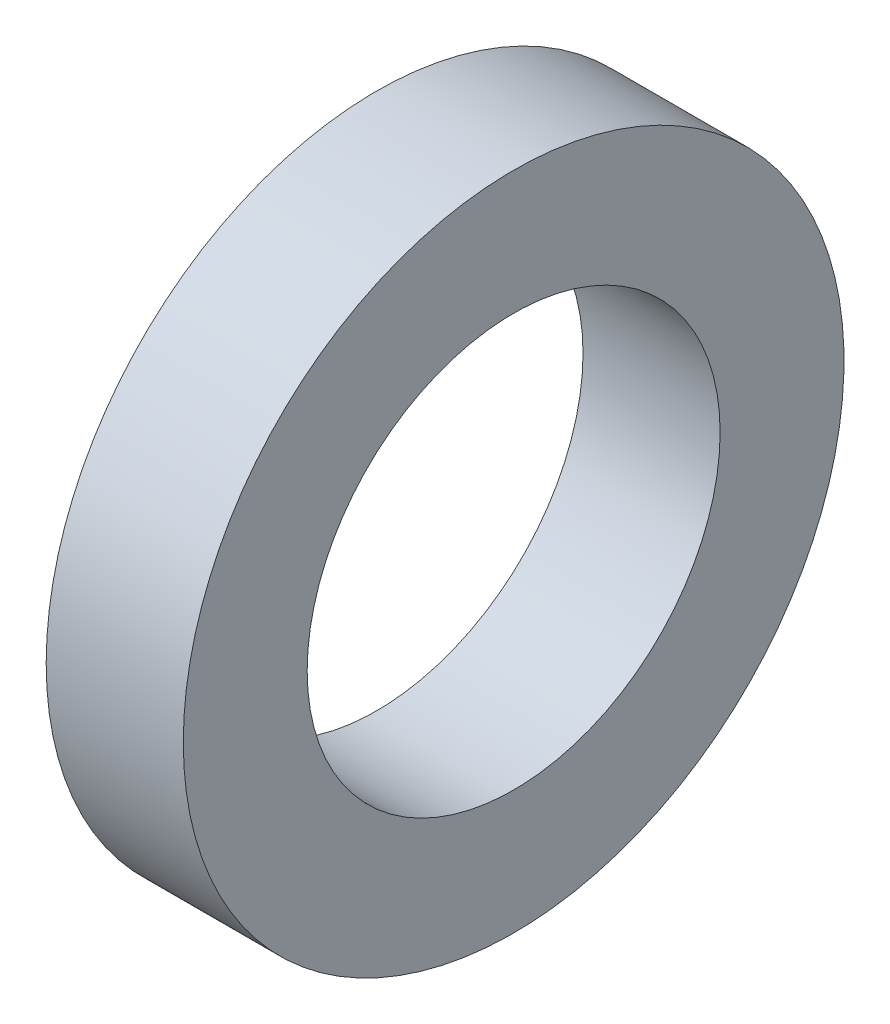
SolidWorks part; units mm, degrees
ref_plane "Front Plane" through (0, 0, 0) normal (0, 0, 1) x (1, 0, 0)
ref_plane "Top Plane" through (0, 0, 0) normal (0, 1, 0) x (1, 0, 0)
ref_plane "Right Plane" through (0, 0, 0) normal (1, 0, 0) x (0, 0, -1)
sketch "Sketch2" plane through (0, 0, 0) normal (0, 0, 1) x (1, 0, 0)
  line L0 (0, 0) -> (58.591, 0) construction
  line L2 (0, 0) -> (18.4, 0)
  line L3 (0, 0) -> (0, 2.5)
  line L4 (0, 2.5) -> (18.4, 2.5)
  line L5 (18.4, 0) -> (18.4, 2.5)
  line L6 (6.0094, 2.5) -> (6.0094, 6)
  line L11 (6.0094, 6) -> (9.9794, 6)
  line L16 (12.9794, 6) -> (12.9794, 3)
  line L17 (12.9794, 3) -> (13.6398, 3)
  line L18 (13.6398, 3) -> (13.6398, 2.5)
  line L19 (13.6398, 2.5) -> (6.0094, 2.5)
  line L22 (13.6398, 2.5) -> (16.1198, 2.5)
  line L23 (13.6398, 2.5) -> (13.6398, 4)
  line L24 (13.6398, 4) -> (16.1198, 4)
  line L25 (16.1198, 2.5) -> (16.1198, 4)
  line L27 (6.0094, 6) -> (9.9794, 6)
  line L28 (6.0094, 6) -> (6.0094, 9)
  line L29 (6.0094, 9) -> (9.9794, 9)
  line L30 (9.9794, 6) -> (9.9794, 9)
  line L31 (6.0094, 9) -> (6.0094, 8.25)
  line L32 (6.0094, 8.25) -> (5.0094, 8.25)
  line L33 (8.6609, 22.001) -> (8.6609, 12.476) construction
  line L34 (5.0094, 12.476) -> (12.3124, 12.476)
  line L35 (9.9794, 9) -> (12.3124, 9)
  line L36 (5.0094, 7.9375) -> (1.7709, 7.9375)
  line L37 (5.0094, 8.25) -> (5.0094, 12.476)
  line L38 (5.0094, 7.9375) -> (5.0094, 13.9365)
  line L39 (5.0094, 13.9365) -> (1.7709, 13.9365)
  line L40 (1.7709, 7.9375) -> (1.7709, 13.9365)
  line L41 (5.0094, 22.001) -> (12.3124, 22.001)
  line L42 (5.0094, 22.001) -> (5.0094, 30.1625)
  line L43 (5.0094, 30.1625) -> (12.3124, 30.1625)
  line L44 (12.3124, 22.001) -> (12.3124, 30.1625)
  line L49 (16.6398, 22.001) -> (16.6398, 7.5)
  line L51 (23.0198, 7.5) -> (23.0198, 6.5)
  line L54 (16.1198, 4) -> (13.6398, 4)
  line L56 (18.0398, 7.5) -> (23.0198, 7.5)
  line L57 (13.3124, 22.001) -> (16.6398, 22.001)
  line L58 (16.1198, 3.5) -> (20.0198, 3.5)
  line L59 (29.9098, 14) -> (26.9098, 11)
  line L60 (4.0094, 31.75) -> (18.0398, 31.75)
  line L61 (18.0398, 7.5) -> (23.0198, 7.5)
  line L62 (18.0398, 7.5) -> (18.0398, 12)
  line L63 (18.0398, 12) -> (23.0198, 12)
  line L64 (23.0198, 7.5) -> (23.0198, 12)
  line L65 (18.0398, 31.75) -> (18.0398, 12)
  line L66 (23.0198, 11) -> (26.9098, 11)
  line L67 (34.8098, 23) -> (31.3098, 19.5)
  line L68 (35.8098, 31) -> (38.7998, 33.99)
  line L69 (29.9098, 14) -> (29.9098, 15)
  line L70 (29.9098, 15) -> (22.9398, 15)
  line L71 (22.9398, 15) -> (21.0398, 15)
  line L72 (18.0398, 7.5) -> (16.6398, 7.5)
  line L73 (21.0398, 15) -> (21.0398, 43)
  line L74 (19.6115, 40) -> (9.6516, 40)
  line L75 (9.6516, 40) -> (4.0094, 40)
  line L76 (21.0398, 43) -> (19.6115, 43)
  line L77 (22.9398, 15) -> (29.9098, 15)
  line L78 (22.9398, 15) -> (22.9398, 21)
  line L79 (22.9398, 21) -> (29.9098, 21)
  line L80 (29.9098, 15) -> (29.9098, 21)
  line L81 (9.6516, 40) -> (19.6115, 40)
  line L82 (9.6516, 40) -> (9.6516, 50)
  line L83 (9.6516, 50) -> (19.6115, 50)
  line L84 (19.6115, 40) -> (19.6115, 50)
  line L85 (4.0094, 40) -> (4.0094, 31.75)
  line L86 (12.9794, 3) -> (12.9794, 2.5)
  line L87 (31.3098, 19.5) -> (29.9098, 19.5)
  line L88 (21.4694, 63.5) -> (21.4694, 51.308)
  line L89 (21.4694, 63.5) -> (25.9398, 63.5)
  line L90 (25.9398, 63.5) -> (25.9398, 25)
  line L91 (27.8398, 25) -> (25.9398, 25)
  line L92 (9.6516, 48) -> (8.2233, 48)
  line L93 (8.2233, 48) -> (8.2233, 53.476)
  line L94 (8.2233, 53.476) -> (19.6115, 53.476)
  line L95 (19.6115, 53.476) -> (19.6115, 50)
  line L96 (13.9174, 63.001) -> (13.9174, 53.476) construction
  line L97 (8.2233, 63.001) -> (19.6115, 63.001)
  line L98 (8.2233, 63.001) -> (8.2233, 68.2625)
  line L99 (8.2233, 68.2625) -> (19.6115, 68.2625)
  line L100 (19.6115, 63.001) -> (19.6115, 68.2625)
  line L101 (12.9794, 6) -> (11.9794, 6)
  line L102 (8.2233, 44.825) -> (4.9848, 44.825)
  line L103 (8.2233, 44.825) -> (8.2233, 54.9365)
  line L104 (8.2233, 54.9365) -> (4.9848, 54.9365)
  line L106 (9.9794, 6) -> (10.8794, 6)
  line L107 (27.8398, 25) -> (34.8098, 25)
  line L108 (34.8098, 25) -> (34.8098, 23)
  line L109 (0, 0) -> (-2, 0)
  line L110 (0, 0) -> (0, 11)
  line L111 (27.8398, 25) -> (34.8098, 25)
  line L112 (27.8398, 25) -> (27.8398, 32.5)
  line L113 (27.8398, 32.5) -> (34.8098, 32.5)
  line L114 (34.8098, 25) -> (34.8098, 32.5)
  line L115 (35.8098, 31) -> (34.8098, 31)
  line L116 (27.8398, 32.5) -> (27.8398, 64.5)
  line L117 (20.5849, 74.025) -> (6.2499, 74.025)
  line L118 (6.2499, 74.025) -> (6.2499, 76.2)
  line L119 (38.7998, 47.29) -> (30.8398, 55.25)
  line L120 (0, 11) -> (-2, 11)
  line L121 (38.7998, 43.815) -> (30.8623, 43.815)
  line L123 (-4.8152, 69.85) -> (1.5348, 76.2)
  line L124 (38.7998, 47.29) -> (38.7998, 33.99)
  line L125 (-2, 0) -> (-2, 11)
  line L126 (38.7998, 37.465) -> (30.8623, 37.465)
  line L127 (30.8623, 43.815) -> (30.8623, 37.465)
  line L128 (6.0094, 2.5) -> (6.0094, 0)
  line L129 (-0.0152, 63.5) -> (-0.0152, 30)
  line L132 (4.9848, 63.5) -> (-0.0152, 63.5)
  line L136 (-1.8152, 30) -> (-11.7752, 30)
  line L138 (-13.7752, 25.4) -> (-2, 25.4)
  line L139 (-2, 25.4) -> (-2, 11.5)
  line L140 (27.8398, 64.5) -> (20.5849, 64.5)
  line L141 (-1.8152, 30) -> (-11.7752, 30)
  line L142 (-1.8152, 30) -> (-1.8152, 39)
  line L143 (-1.8152, 39) -> (-11.7752, 39)
  line L144 (-11.7752, 30) -> (-11.7752, 39)
  line L145 (20.5849, 64.5) -> (20.5849, 74.025)
  line L146 (-12.7752, 37) -> (-12.7752, 47.29)
  line L147 (-12.7752, 37) -> (-11.7752, 37)
  line L148 (30.8398, 55.25) -> (30.8398, 76.2)
  line L149 (11.9794, 6) -> (11.9794, 5.45)
  line L154 (-2, 11.5) -> (0.5, 11.5)
  line L155 (4.9848, 60.6197) -> (24.0348, 60.6197)
  line L160 (4.9848, 60.6197) -> (4.9848, 55.8572)
  line L161 (4.9848, 55.8572) -> (24.0348, 55.8572)
  line L166 (24.0348, 60.6197) -> (24.0348, 55.8572)
  line L167 (4.9848, 60.6197) -> (24.0348, 55.8572) construction
  line L172 (4.9848, 55.8572) -> (24.0348, 60.6197) construction
  line L173 (24.0348, 62.2072) -> (25.9398, 62.2072)
  line L174 (11.9794, 5.45) -> (10.8794, 5.45)
  line L175 (10.8794, 6) -> (10.8794, 5.45)
  line L176 (24.0348, 62.2072) -> (24.0348, 54.2697)
  line L177 (24.0348, 54.2697) -> (25.9398, 54.2697)
  line L178 (25.9398, 62.2072) -> (25.9398, 54.2697)
  line L179 (24.0348, 62.2072) -> (25.9398, 54.2697) construction
  line L180 (24.0348, 54.2697) -> (25.9398, 62.2072) construction
  line L181 (3, 19.6197) -> (15.7, 19.6197)
  line L182 (3, 19.6197) -> (3, 14.8572)
  line L183 (3, 14.8572) -> (15.7, 14.8572)
  line L184 (15.7, 19.6197) -> (15.7, 14.8572)
  line L185 (3, 19.6197) -> (15.7, 14.8572) construction
  line L186 (3, 14.8572) -> (15.7, 19.6197) construction
  line L187 (15.7, 21.2072) -> (16.6398, 21.2072)
  line L188 (15.7, 21.2072) -> (15.7, 13.2697)
  line L189 (15.7, 13.2697) -> (16.6398, 13.2697)
  line L190 (16.6398, 21.2072) -> (16.6398, 13.2697)
  line L191 (15.7, 21.2072) -> (16.6398, 13.2697) construction
  line L192 (15.7, 13.2697) -> (16.6398, 21.2072) construction
  line L193 (0.5, 11.5) -> (0.5, 6.9375)
  line L194 (0.5, 6.9375) -> (1.7709, 6.9375)
  line L195 (23.0198, 6.5) -> (20.0198, 3.5)
  line L196 (4.9848, 63.5) -> (4.9848, 54.9365)
  line L197 (3, 43.825) -> (4.9848, 43.825)
  line L198 (1.7709, 6.9375) -> (1.7709, 7.9375)
  line L199 (6.0094, 0) -> (12.9794, 0)
  line L200 (12.9794, 0) -> (12.9794, 2.5)
  line L201 (18.0398, 31.75) -> (18.0398, 35.875)
  line L202 (18.0398, 35.875) -> (21.0398, 35.875)
  line L203 (30.8398, 76.2) -> (6.2499, 76.2)
  line L204 (2.8049, 69.85) -> (7.2499, 69.85) construction
  line L205 (7.2499, 67.4688) -> (26.2999, 67.4688)
  line L206 (7.2499, 74.025) -> (7.2499, 64.5)
  line L207 (7.2499, 64.5) -> (-1.8152, 64.5)
  line L208 (-1.8152, 64.5) -> (-1.8152, 39)
  line L209 (-12.7752, 47.29) -> (-4.8152, 55.25)
  line L210 (-4.8152, 55.25) -> (-4.8152, 69.85)
  line L211 (7.2499, 67.4688) -> (7.2499, 72.2312)
  line L212 (7.2499, 72.2312) -> (26.2999, 72.2313)
  line L213 (26.2999, 67.4688) -> (26.2999, 72.2313)
  line L214 (26.2999, 73.8187) -> (30.8398, 73.8187)
  line L215 (26.2999, 73.8187) -> (26.2999, 65.8813)
  line L216 (26.2999, 65.8813) -> (30.8398, 65.8813)
  line L217 (30.8398, 73.8187) -> (30.8398, 65.8813)
  line L218 (2.8049, 72.2313) -> (25.0299, 72.2313)
  line L219 (2.8049, 72.2313) -> (2.8049, 67.4687)
  line L220 (2.8049, 67.4687) -> (25.0299, 67.4687)
  line L221 (25.0299, 72.2313) -> (25.0299, 67.4687)
  line L222 (25.0299, 69.85) -> (20.5849, 69.85) construction
  line L223 (21.4694, 51.308) -> (22.9398, 51.308)
  line L224 (22.9398, 51.308) -> (22.9398, 21)
  line L225 (13.6398, 4) -> (13.6398, 12.2697)
  line L226 (13.6398, 12.2697) -> (13.3124, 12.2697)
  line L227 (13.3124, 12.2697) -> (13.3124, 22.001)
  line L228 (12.3124, 9) -> (12.3124, 12.476)
  line L229 (-1.8152, 30) -> (-0.0152, 30)
  line L230 (8.2233, 65.6317) -> (2.8049, 65.6317) construction
  line L231 (19.6115, 65.6317) -> (25.0299, 65.6317) construction
  line L232 (1.5348, 76.2) -> (6.2499, 76.2)
  line L233 (-11.7752, 30) -> (-13.7752, 30)
  line L234 (-13.7752, 30) -> (-13.7752, 25.4)
  line L235 (3, 13.9365) -> (3, 43.825)
  line L236 (4.9848, 54.9365) -> (4.9848, 44.825)
  line L237 (4.9848, 43.825) -> (4.9848, 44.825)
  circle A0 centre (26.8898, 25.95) radius 0.95
  circle A1 centre (21.9898, 15.95) radius 0.95
  circle A2 centre (17.3398, 8.2) radius 0.7
  circle A3 centre (10.4294, 6.45) radius 0.45
  circle A4 centre (-0.9152, 30.9) radius 0.9
  point P7 (24.9873, 58.2385)
  point P131 (16.1699, 17.2385)
  point P135 (14.5098, 58.2385)
  point P146 (9.35, 17.2385)
sketch "Sketch3" plane through (0, 0, 0) normal (0, 0, 1) x (1, 0, 0)
  line L0 (18.0398, 12) -> (23.0198, 12) construction
  line L1 (18.0398, 7.5) -> (23.0198, 7.5) construction
  line L2 (18.0398, 7.5) -> (18.0398, 12) construction
  line L3 (23.0198, 7.5) -> (23.0198, 12) construction
  line L4 (18.0398, 12) -> (23.0198, 12)
  line L5 (18.0398, 7.5) -> (23.0198, 7.5)
  line L6 (18.0398, 7.5) -> (18.0398, 12)
  line L7 (23.0198, 7.5) -> (23.0198, 12)
revolve "Revolve1" add sketch "Sketch3" angle 360 about L0
